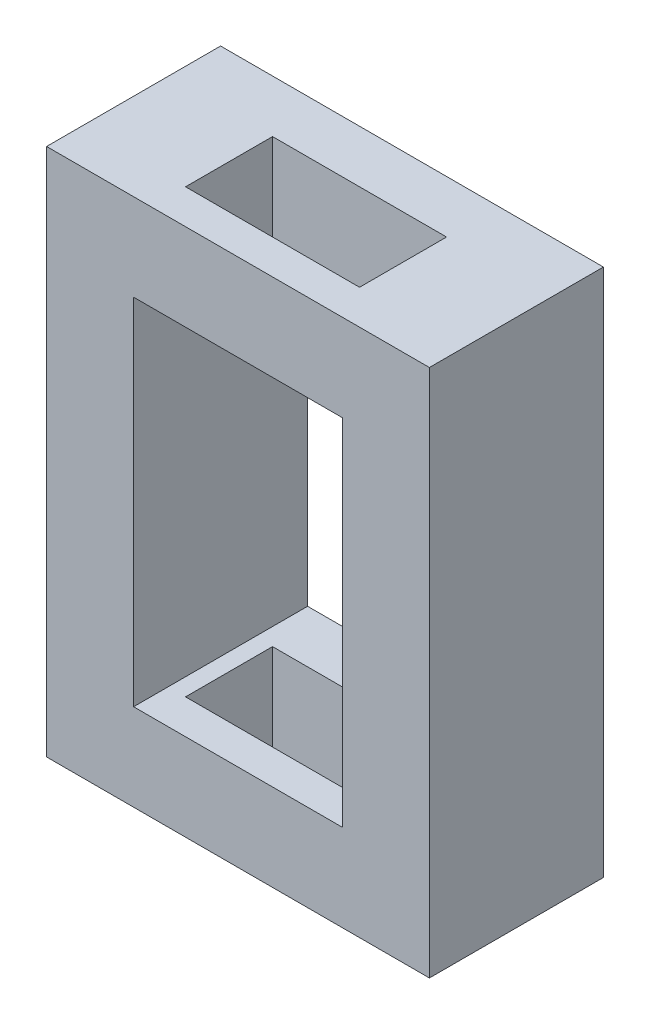
SolidWorks part; units mm, degrees
ref_plane "Front Plane" through (0, 0, 0) normal (0, 0, 1) x (1, 0, 0)
ref_plane "Top Plane" through (0, 0, 0) normal (0, 1, 0) x (1, 0, 0)
ref_plane "Right Plane" through (0, 0, 0) normal (1, 0, 0) x (0, 0, -1)
sketch "Sketch2" plane through (0, 0, 0) normal (0, 0, 1) x (1, 0, 0)
  line L1 (-10.9973, 10.4978) -> (0.0027, 10.4978)
  line L2 (-10.9973, 10.4978) -> (-10.9973, -4.6945)
  line L3 (-10.9973, -4.6945) -> (0.0027, -4.6945)
  line L4 (0.0027, 10.4978) -> (0.0027, -4.6945)
  line L5 (-8.4973, 7.9978) -> (-2.4973, 7.9978)
  line L6 (-8.4973, 7.9978) -> (-8.4973, -2.1945)
  line L7 (-8.4973, -2.1945) -> (-2.4973, -2.1945)
  line L8 (-2.4973, 7.9978) -> (-2.4973, -2.1945)
  dimension "D1" = 2.5
  dimension "D2" = 2.5
  dimension "D3" = 2.5
  dimension "D4" = 2.5
  dimension "D5" = 11
extrude "Boss-Extrude1" add sketch "Sketch2" along normal blind 5
sketch "Sketch3" plane through (0, 10.4978, 0) normal (0, 1, 0) x (1, 0, 0)
  line L0 (0.0027, -5) -> (0.0027, 0) construction
  line L1 (-7.9973, -1.5071) -> (-2.9973, -1.5071)
  line L2 (-7.9973, -1.5071) -> (-7.9973, -4.0071)
  line L3 (-7.9973, -4.0071) -> (-2.9973, -4.0071)
  line L4 (-2.9973, -1.5071) -> (-2.9973, -4.0071)
  dimension "D1" = 2.5
  dimension "D2" = 5
  dimension "D3" = 3
extrude "Cut-Extrude1" cut sketch "Sketch3" against normal blind 16
